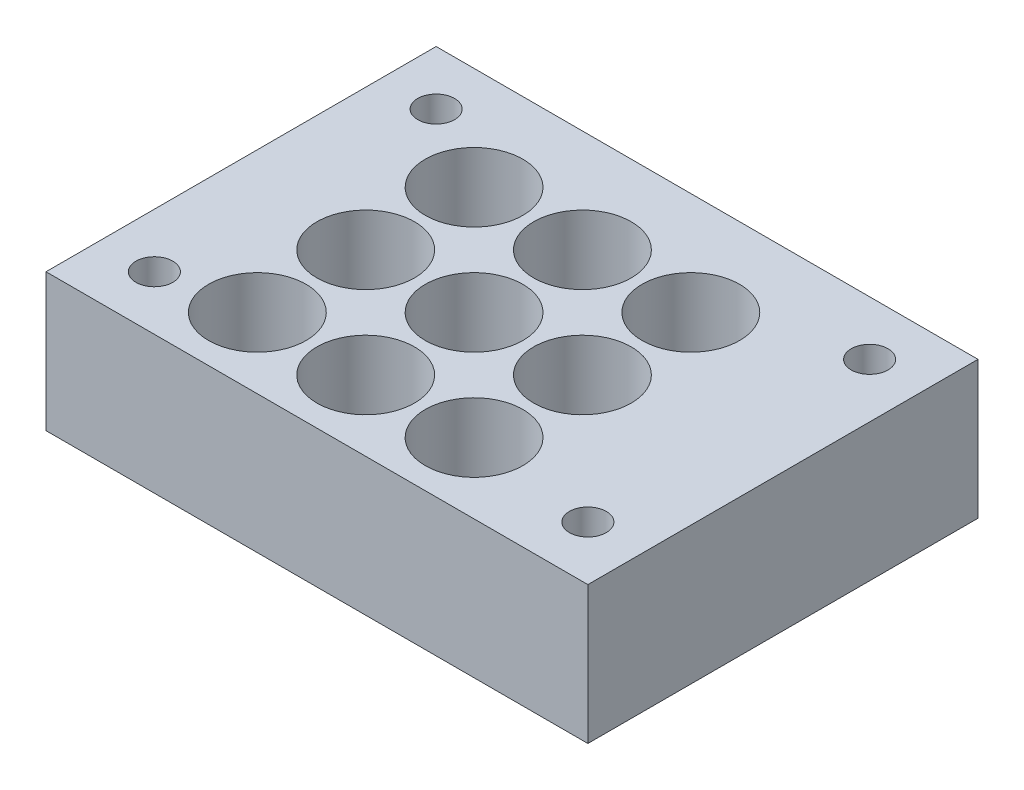
SolidWorks part; units mm, degrees
ref_plane "Front Plane" through (0, 0, 0) normal (0, 0, 1) x (1, 0, 0)
ref_plane "Top Plane" through (0, 0, 0) normal (0, 1, 0) x (1, 0, 0)
ref_plane "Right Plane" through (0, 0, 0) normal (1, 0, 0) x (0, 0, -1)
sketch "Sketch1" plane through (0, 0, 0) normal (0, 1, 0) x (1, 0, 0)
  line L0 (45, 31) -> (5, 31) construction
  line L1 (0, 0) -> (50, 0)
  line L2 (0, 0) -> (0, 36)
  line L3 (0, 36) -> (50, 36)
  line L4 (50, 0) -> (50, 36)
  line L6 (45, 31) -> (45, 5) construction
  circle A19 centre (13, 6.5) radius 4.5
  circle A28 centre (5, 5) radius 1.7
  circle A29 centre (5, 31) radius 1.7
  circle A30 centre (45, 31) radius 1.7
  circle A31 centre (45, 5) radius 1.7
  circle A32 centre (23, 6.5) radius 4.5
  circle A33 centre (33, 6.5) radius 4.5
  circle A34 centre (23, 16.5) radius 4.5
  circle A35 centre (33, 16.5) radius 4.5
  circle A36 centre (23, 26.5) radius 4.5
  circle A37 centre (33, 26.5) radius 4.5
  circle A38 centre (13, 16.5) radius 4.5
  circle A39 centre (13, 26.5) radius 4.5
  point P7 (45, 18)
  point P9 (25, 31)
  point P10 (25, 36)
  point P20 (50, 18)
  dimension "D5" = 40
  dimension "D6" = 26
  dimension "D3" = 9
  dimension "D8" = 3.4
  dimension "D1" = 50
  dimension "D2" = 36
  dimension "D4" = 8
  dimension "D7" = 1.5
  dimension "D9" = 3
extrude "Boss-Extrude1" add sketch "Sketch1" along normal blind 12.7
equation "\"o\"= 10mm"
equation "\"P\"= 10"
